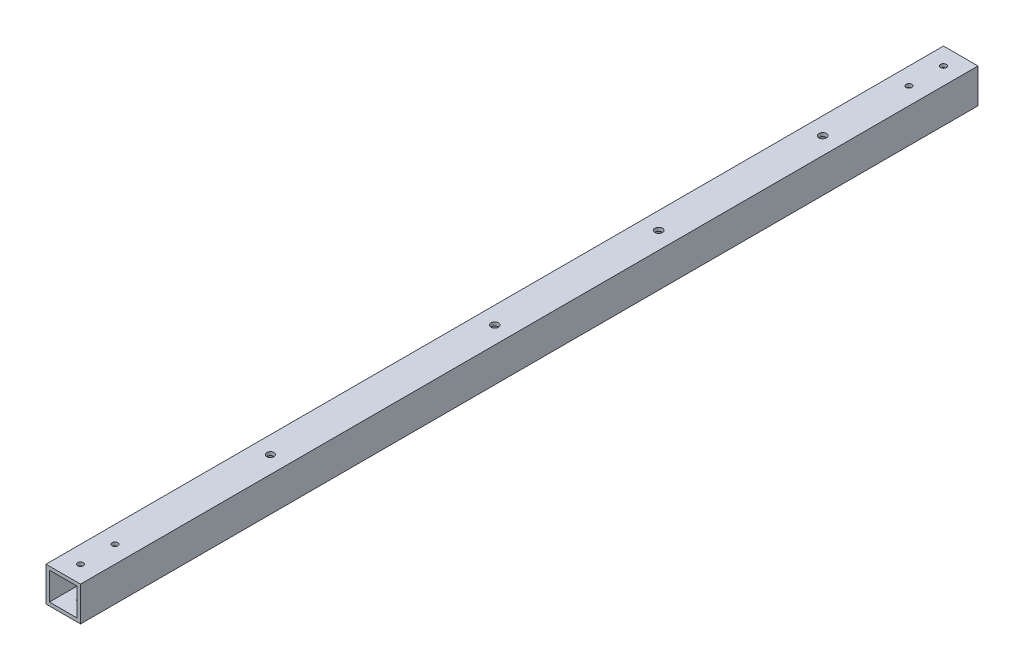
SolidWorks part; units mm, degrees
ref_plane "正面" through (0, 0, 0) normal (0, 0, 1) x (1, 0, 0)
ref_plane "平面" through (0, 0, 0) normal (0, 1, 0) x (1, 0, 0)
ref_plane "右側面" through (0, 0, 0) normal (1, 0, 0) x (0, 0, -1)
sketch "ｽｹｯﾁ1" plane through (0, 0, 0) normal (0, 0, 1) x (1, 0, 0)
  line L1 (-10, 10) -> (10, 10)
  line L2 (-10, 10) -> (-10, -10)
  line L3 (-10, -10) -> (10, -10)
  line L4 (10, 10) -> (10, -10)
  line L5 (-10, 10) -> (10, -10) construction
  line L6 (-10, -10) -> (10, 10) construction
  line L7 (-8, 8) -> (8, 8)
  line L8 (-8, 8) -> (-8, -8)
  line L9 (-8, -8) -> (8, -8)
  line L10 (8, 8) -> (8, -8)
  line L11 (-8, 8) -> (8, -8) construction
  line L12 (-8, -8) -> (8, 8) construction
  point P0 (0, 0)
  point P6 (0, 0)
  dimension "D1" = 20
  dimension "D2" = 20
  dimension "D3" = 16
  dimension "D4" = 16
extrude "ﾎﾞｽ - 押し出し1" add sketch "ｽｹｯﾁ1" along normal blind 560
sketch "ｽｹｯﾁ3" plane through (10, 0, 0) normal (1, 0, 0) x (0, 0, -1)
  line L0 (-560, 0) -> (-530, 0)
  line L1 (-560, -10) -> (-560, 10) construction
  line L2 (-530, 0) -> (-30, 0)
  circle A0 centre (-530, 0) radius 2.2
  circle A1 centre (-30, 0) radius 2.2
  dimension "D2" = 4.4
  dimension "D4" = 4.4
  dimension "D1" = 30
  dimension "D3" = 500
sketch "ｽｹｯﾁ4" plane through (0, 10, 0) normal (0, 1, 0) x (1, 0, 0)
  line L0 (0, -560) -> (0, -550)
  line L1 (10, -560) -> (-10, -560) construction
  line L2 (0, -550) -> (0, -10)
  circle A0 centre (0, -550) radius 2.2
  circle A1 centre (0, -10) radius 2.2
  dimension "D2" = 4.4
  dimension "D4" = 4.4
  dimension "D1" = 10
  dimension "D3" = 540
extrude "ｶｯﾄ - 押し出し3" cut sketch "ｽｹｯﾁ4" against normal blind 560
sketch "ｽｹｯﾁ5" plane through (0, 0, 0) normal (0, 0, -1) x (-1, 0, 0)
  line L0 (10, 10) -> (10, -10) construction
  line L1 (-10, -10) -> (10, -10)
  line L2 (-10, -10) -> (-10, 10)
  line L3 (-10, 10) -> (10, 10)
  line L4 (10, -10) -> (10, 10)
  line L5 (-10, -10) -> (10, 10) construction
  line L6 (-10, 10) -> (10, -10) construction
  line L8 (-8, -8) -> (8, -8)
  line L9 (-8, -8) -> (-8, 8)
  line L10 (-8, 8) -> (8, 8)
  line L11 (8, -8) -> (8, 8)
  line L12 (-8, -8) -> (8, 8) construction
  line L13 (-8, 8) -> (8, -8) construction
  point P1 (0, 0)
  point P8 (0, 0)
extrude "ﾎﾞｽ - 押し出し2" add sketch "ｽｹｯﾁ5" along normal blind 20
sketch "ｽｹｯﾁ6" plane through (0, 0, 560) normal (0, 0, 1) x (1, 0, 0)
  line L1 (10, -10) -> (-10, -10)
  line L2 (10, -10) -> (10, 10)
  line L3 (10, 10) -> (-10, 10)
  line L4 (-10, -10) -> (-10, 10)
  line L5 (10, -10) -> (-10, 10) construction
  line L6 (10, 10) -> (-10, -10) construction
  line L7 (8, -8) -> (-8, -8)
  line L8 (8, -8) -> (8, 8)
  line L9 (8, 8) -> (-8, 8)
  line L10 (-8, -8) -> (-8, 8)
  line L11 (8, -8) -> (-8, 8) construction
  line L12 (8, 8) -> (-8, -8) construction
  point P0 (0, 0)
  point P7 (0, 0)
extrude "ﾎﾞｽ - 押し出し3" add sketch "ｽｹｯﾁ6" along normal blind 20
sketch "ｽｹｯﾁ8" plane through (10, 0, 0) normal (1, 0, 0) x (0, 0, -1)
  line L0 (20, 0) -> (10, 0)
  line L1 (20, 10) -> (20, -10) construction
  line L2 (-580, 0) -> (-570, 0)
  line L3 (-580, -10) -> (-580, 10) construction
  circle A0 centre (10, 0) radius 2.2
  circle A1 centre (-570, 0) radius 2.2
  dimension "D2" = 4.4
  dimension "D4" = 4.4
  dimension "D1" = 10
  dimension "D3" = 10
extrude "ｶｯﾄ - 押し出し4" cut sketch "ｽｹｯﾁ8" against normal blind 20 contours A1
sketch "ｽｹｯﾁ9" plane through (10, 0, 0) normal (1, 0, 0) x (0, 0, -1)
  line L0 (20, 0) -> (10, 0)
  line L1 (20, 10) -> (20, -10) construction
  circle A0 centre (10, 0) radius 2.2
  dimension "D2" = 4.4
  dimension "D1" = 10
extrude "ｶｯﾄ - 押し出し5" cut sketch "ｽｹｯﾁ9" against normal blind 20
sketch "ｽｹｯﾁ10" plane through (0, 0, -20) normal (0, 0, -1) x (-1, 0, 0)
  line L1 (25.7112, -15.2204) -> (-25.7112, -15.2204)
  line L2 (25.7112, -15.2204) -> (25.7112, 15.2204)
  line L3 (25.7112, 15.2204) -> (-25.7112, 15.2204)
  line L4 (-25.7112, -15.2204) -> (-25.7112, 15.2204)
  line L5 (25.7112, -15.2204) -> (-25.7112, 15.2204) construction
  line L6 (25.7112, 15.2204) -> (-25.7112, -15.2204) construction
  point P0 (0, 0)
extrude "ｶｯﾄ - 押し出し6" cut sketch "ｽｹｯﾁ10" against normal blind 40
sketch "ｽｹｯﾁ11" plane through (0, 0, 580) normal (0, 0, 1) x (1, 0, 0)
  line L1 (19.6813, -26.3737) -> (-19.6813, -26.3737)
  line L2 (19.6813, -26.3737) -> (19.6813, 26.3737)
  line L3 (19.6813, 26.3737) -> (-19.6813, 26.3737)
  line L4 (-19.6813, -26.3737) -> (-19.6813, 26.3737)
  line L5 (19.6813, -26.3737) -> (-19.6813, 26.3737) construction
  line L6 (19.6813, 26.3737) -> (-19.6813, -26.3737) construction
  point P0 (0, 0)
extrude "ｶｯﾄ - 押し出し7" cut sketch "ｽｹｯﾁ11" against normal blind 40
sketch "ｽｹｯﾁ12" plane through (0, -10, 0) normal (0, -1, 0) x (-1, 0, 0)
  line L0 (0, -540) -> (0, -530)
  line L1 (10, -540) -> (-10, -540) construction
  line L2 (0, -530) -> (0, -510)
  circle A0 centre (0, -530) radius 1
  circle A1 centre (0, -510) radius 1
  dimension "D3" = 2
  dimension "D4" = 2
  dimension "D1" = 10
  dimension "D2" = 20
extrude "ｶｯﾄ - 押し出し8" cut sketch "ｽｹｯﾁ12" against normal blind 20
sketch "ｽｹｯﾁ13" plane through (0, -10, 0) normal (0, -1, 0) x (-1, 0, 0)
  line L0 (0, -20) -> (0, -30)
  line L1 (-10, -20) -> (10, -20) construction
  line L2 (0, -30) -> (0, -50)
  circle A0 centre (0, -30) radius 1
  circle A1 centre (0, -50) radius 1
  dimension "D3" = 2
  dimension "D4" = 2
  dimension "D1" = 10
  dimension "D2" = 20
extrude "ｶｯﾄ - 押し出し9" cut sketch "ｽｹｯﾁ13" against normal blind 20
sketch "ｽｹｯﾁ15" plane through (0, -10, 0) normal (0, -1, 0) x (1, 0, 0)
  line L0 (0, 20) -> (0, 100)
  line L1 (10, 20) -> (-10, 20) construction
  line L2 (0, 100) -> (0, 195)
  line L3 (0, 195) -> (0, 290)
  circle A0 centre (0, 100) radius 2.2
  circle A1 centre (0, 195) radius 2.2
  circle A2 centre (0, 290) radius 2.2
  dimension "D2" = 4.4
  dimension "D5" = 4.4
  dimension "D6" = 4.4
  dimension "D1" = 80
  dimension "D3" = 95
  dimension "D4" = 95
extrude "ｶｯﾄ - 押し出し11" cut sketch "ｽｹｯﾁ15" against normal through all
sketch "ｽｹｯﾁ16" plane through (0, -10, 0) normal (0, -1, 0) x (1, 0, 0)
  line L0 (0, 510) -> (0, 420)
  circle A0 centre (0, 420) radius 2.1
  dimension "D2" = 4.2
  dimension "D1" = 90
extrude "ｶｯﾄ - 押し出し12" cut sketch "ｽｹｯﾁ16" against normal through all
hole_wizard "M4x0.7 ねじ穴4" positions "3Dｽｹｯﾁ4" profile "ｽｹｯﾁ20" tap size "M4x0.7" standard "JIS" end condition through all
sketch3d "3Dｽｹｯﾁ4"
  line L0 (0, -8, 30) -> (0, -10, 30) construction
  line L1 (0, -8, 50) -> (0, -10, 50) construction
  point P0 (0, -10, 30)
  point P4 (0, -10, 50)
sketch "ｽｹｯﾁ20" plane through (0, -10, 30) normal (1, 0, 0) x (0, 0, -1)
  line L0 (0, 0) -> (0, 20)
  line L1 (0, 20) -> (1.65, 20)
  line L2 (1.65, 20) -> (1.65, 0)
  line L5 (1.65, 0) -> (0, 0)
  line L11 (0, -6.35) -> (0, 107.95) construction
  dimension "次ｻｰﾌｪｽまでのねじ下穴ﾄﾞﾘﾙ直径" = 3.3
  dimension "次ｻｰﾌｪｽまでのねじ下穴ﾄﾞﾘﾙの深さ" = 20
cosmetic thread "穴のねじ山7" parameters "D2"=4
cosmetic thread "穴のねじ山8" parameters "D2"=4
hole_wizard "M4x0.7 ねじ穴5" positions "3Dｽｹｯﾁ5" profile "ｽｹｯﾁ21" tap size "M4x0.7" standard "JIS" end condition through all
sketch3d "3Dｽｹｯﾁ5"
  line L0 (0, -8, 530) -> (0, -10, 530) construction
  line L1 (0, -8, 510) -> (0, -10, 510) construction
  point P0 (0, -10, 530)
  point P4 (0, -10, 510)
sketch "ｽｹｯﾁ21" plane through (0, -10, 530) normal (1, 0, 0) x (0, 0, -1)
  line L0 (0, 0) -> (0, 20)
  line L1 (0, 20) -> (1.65, 20)
  line L2 (1.65, 20) -> (1.65, 0)
  line L5 (1.65, 0) -> (0, 0)
  line L11 (0, -6.35) -> (0, 107.95) construction
  dimension "次ｻｰﾌｪｽまでのねじ下穴ﾄﾞﾘﾙ直径" = 3.3
  dimension "次ｻｰﾌｪｽまでのねじ下穴ﾄﾞﾘﾙの深さ" = 20
cosmetic thread "穴のねじ山9" parameters "D2"=4
cosmetic thread "穴のねじ山10" parameters "D2"=4
